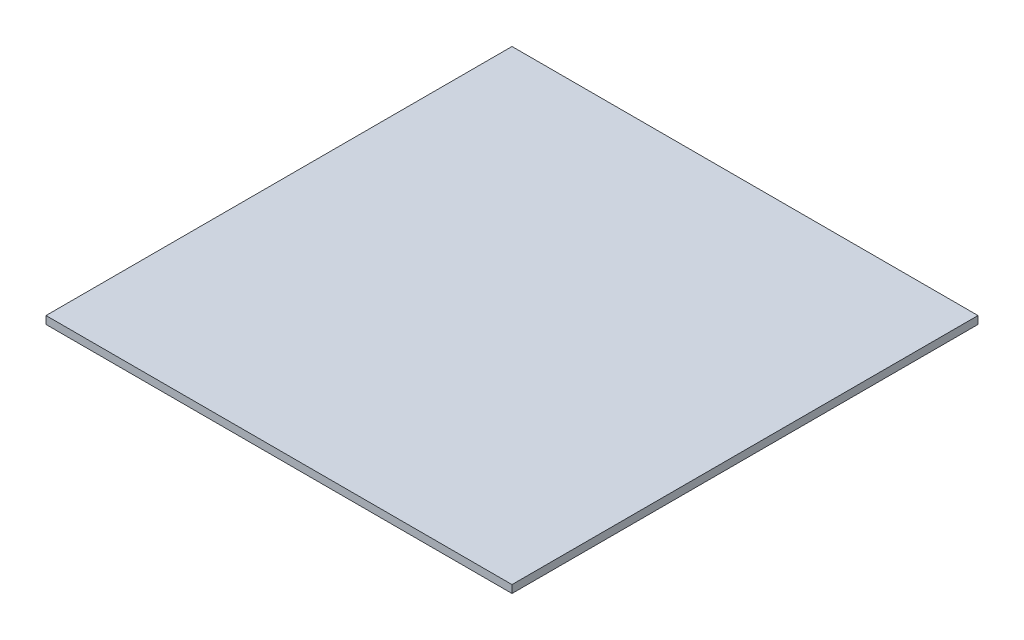
SolidWorks part; units mm, degrees
material "PVC Rigid"
ref_plane "Front Plane" through (0, 0, 0) normal (0, 0, 1) x (1, 0, 0)
ref_plane "Top Plane" through (0, 0, 0) normal (0, 1, 0) x (1, 0, 0)
ref_plane "Right Plane" through (0, 0, 0) normal (1, 0, 0) x (0, 0, -1)
sketch "Sketch1" plane through (0, 0, 0) normal (0, 1, 0) x (1, 0, 0)
  line L0 (-95.25, 95.25) -> (95.25, -95.25) construction
  line L1 (-95.25, 95.25) -> (95.25, 95.25)
  line L2 (-95.25, 95.25) -> (-95.25, -95.25)
  line L3 (-95.25, -95.25) -> (95.25, -95.25)
  line L4 (95.25, 95.25) -> (95.25, -95.25)
  dimension "D1" = 190.5
extrude "Boss-Extrude1" add sketch "Sketch1" along normal blind 3.175
